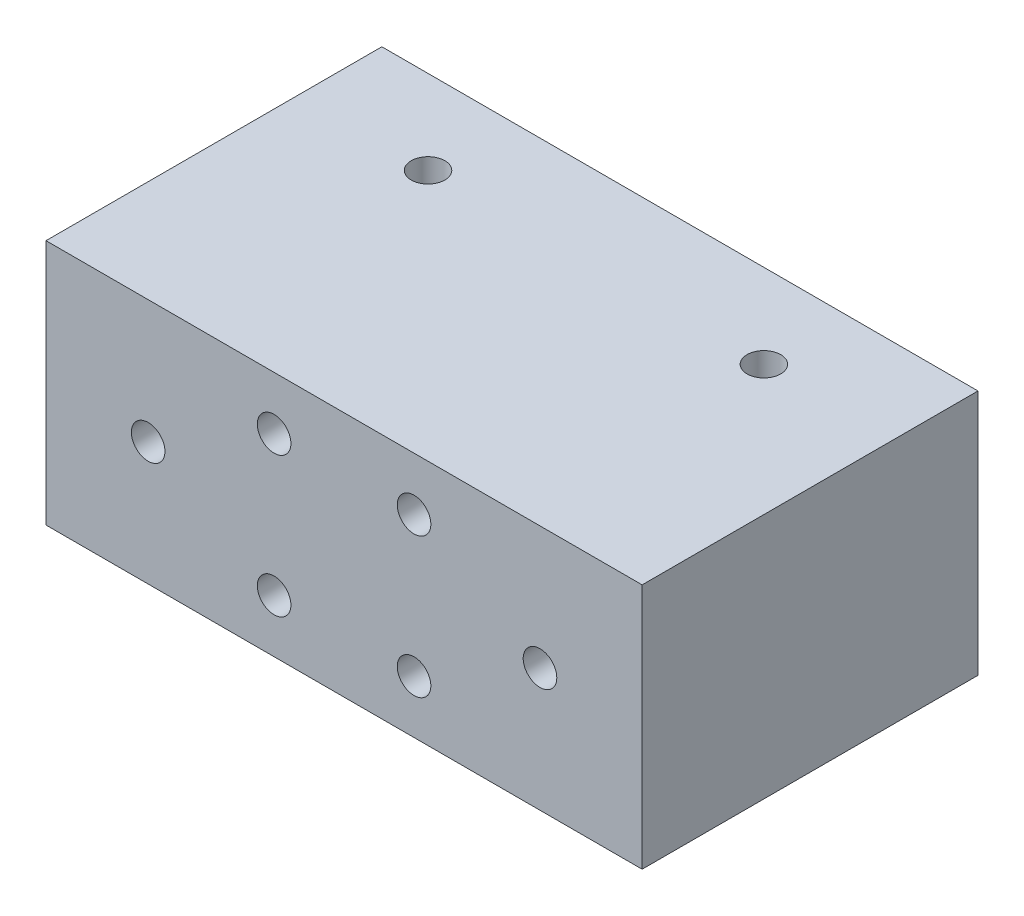
SolidWorks part; units mm, degrees
ref_plane "Alzado" through (0, 0, 0) normal (0, 0, 1) x (1, 0, 0)
ref_plane "Planta" through (0, 0, 0) normal (0, 1, 0) x (1, 0, 0)
ref_plane "Vista lateral" through (0, 0, 0) normal (1, 0, 0) x (0, 0, -1)
sketch "Croquis1" plane through (0, 0, 0) normal (0, 0, 1) x (1, 0, 0)
  line L1 (-21.3, -8.8) -> (21.3, -8.8)
  line L2 (-21.3, -8.8) -> (-21.3, 8.8)
  line L3 (-21.3, 8.8) -> (21.3, 8.8)
  line L4 (21.3, -8.8) -> (21.3, 8.8)
  line L5 (-21.3, -8.8) -> (21.3, 8.8) construction
  line L6 (-21.3, 8.8) -> (21.3, -8.8) construction
  point P0 (0, 0)
extrude "Saliente-Extruir1" add sketch "Croquis1" along normal blind 24
sketch "Croquis2" plane through (0, 8.8, 0) normal (0, 1, 0) x (1, 0, 0)
  line L0 (21.3, -24) -> (-21.3, -24) construction
  line L5 (12, -42) -> (-12, -6) construction
  line L6 (12, -6) -> (-12, -42) construction
  circle A0 centre (-12, -6) radius 1.2
  circle A1 centre (12, -6) radius 1.2
  point P0 (0, -24)
extrude "Cortar-Extruir1" cut sketch "Croquis2" against normal blind 24
sketch "Croquis4" plane through (0, 0, 24) normal (0, 0, 1) x (1, 0, 0)
  circle A0 centre (-14, 0) radius 1.2
  circle A1 centre (-5, 5) radius 1.2
  circle A2 centre (5, 5) radius 1.2
  circle A3 centre (14, 0) radius 1.2
  circle A4 centre (5, -5) radius 1.2
  circle A5 centre (-5, -5) radius 1.2
extrude "Cortar-Extruir2" cut sketch "Croquis4" against normal blind 10
